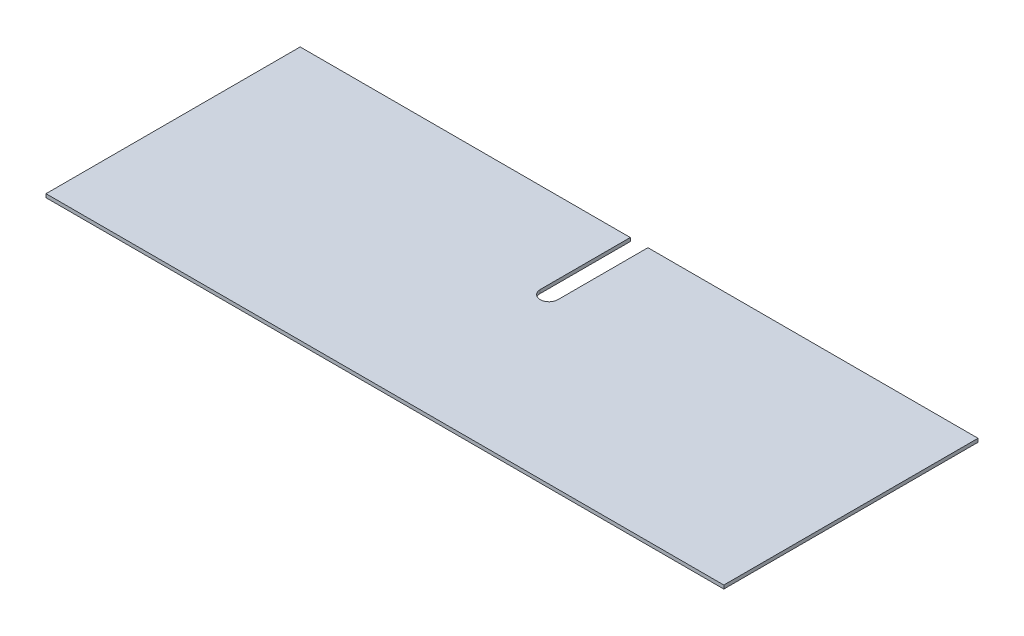
SolidWorks part; units mm, degrees
material "PE High Density"
ref_plane "Front Plane" through (0, 0, 0) normal (0, 0, 1) x (1, 0, 0)
ref_plane "Top Plane" through (0, 0, 0) normal (0, 1, 0) x (1, 0, 0)
ref_plane "Right Plane" through (0, 0, 0) normal (1, 0, 0) x (0, 0, -1)
sketch "Sketch1" plane through (0, 0, 0) normal (0, 1, 0) x (1, 0, 0)
  line L1 (0, 0) -> (609.6, 0)
  line L2 (0, 0) -> (0, 228.6)
  line L3 (0, 228.6) -> (609.6, 228.6)
  line L4 (609.6, 0) -> (609.6, 228.6)
  dimension "D1" = 228.6
  dimension "D2" = 609.6
extrude "Boss-Extrude1" add sketch "Sketch1" along normal blind 3.175
sketch "Sketch2" plane through (0, 3.175, 0) normal (0, 1, 0) x (1, 0, 0)
  line L0 (609.6, 228.6) -> (0, 228.6) construction
  line L1 (296.8625, 228.6) -> (312.7375, 228.6)
  line L2 (296.8625, 228.6) -> (296.8625, 147.6375)
  line L4 (312.7375, 228.6) -> (312.7375, 147.6375)
  line L5 (0, 228.6) -> (0, 0) construction
  arc A0 (296.8625, 147.6375) -> (312.7375, 147.6375) centre (304.8, 147.6375) ccw
  dimension "D1" = 80.9625
  dimension "D2" = 15.875
  dimension "D3" = 304.8
extrude "Cut-Extrude1" cut sketch "Sketch2" against normal through all
